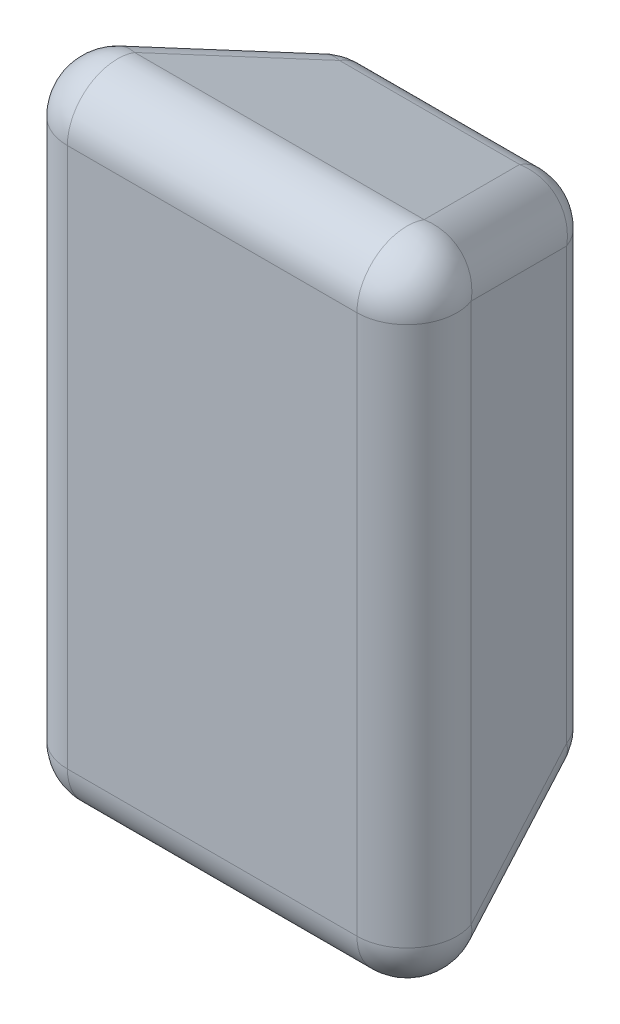
SolidWorks part; units mm, degrees
ref_plane "Plan de face" through (0, 0, 0) normal (0, 0, 1) x (1, 0, 0)
ref_plane "Plan de dessus" through (0, 0, 0) normal (0, 1, 0) x (1, 0, 0)
ref_plane "Plan de droite" through (0, 0, 0) normal (1, 0, 0) x (0, 0, -1)
sketch "Esquisse1" plane through (0, 0, 0) normal (0, 0, 1) x (1, 0, 0)
  line L1 (-28.2934, -54.2372) -> (21.7066, -54.2372)
  line L2 (-28.2934, -54.2372) -> (-28.2934, -154.2372)
  line L3 (-28.2934, -154.2372) -> (21.7066, -154.2372)
  line L4 (21.7066, -54.2372) -> (21.7066, -154.2372)
extrude "Boss.-Extru.1" add sketch "Esquisse1" along normal blind 50 draft 20 contours L1 L4 L3 L2 draft outward yes
fillet "Congé1" radius 10 12 edges at (-46.492, -104.2372, 50) (-3.2934, -172.4357, 50) (-37.3927, -163.3365, 25) (-28.2934, -104.2372, 0) (-3.2934, -154.2372, 0) (21.7066, -104.2372, 0) (-3.2934, -54.2372, 0) (39.9051, -104.2372, 50) (-3.2934, -36.0387, 50) (-37.3927, -45.1379, 25) (30.8058, -45.1379, 25) (30.8058, -163.3365, 25)
